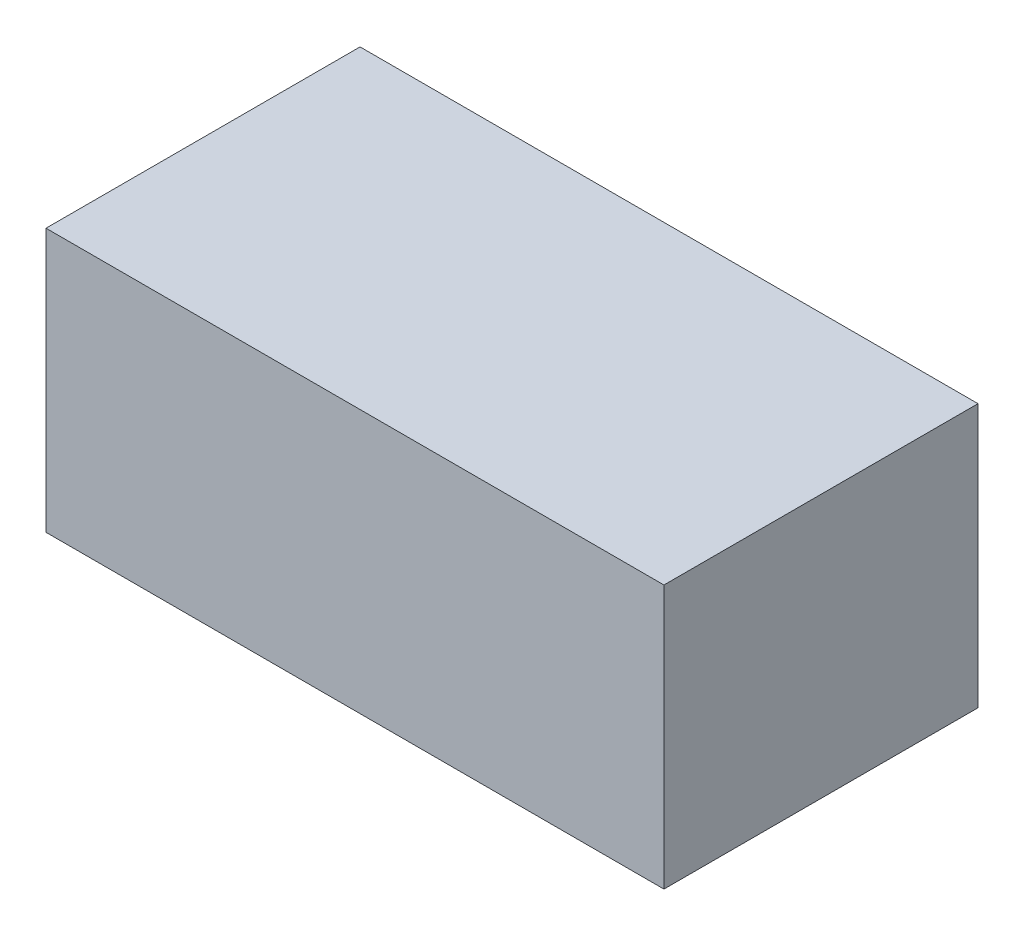
SolidWorks part; units mm, degrees
ref_plane "Front Plane" through (0, 0, 0) normal (0, 0, 1) x (1, 0, 0)
ref_plane "Top Plane" through (0, 0, 0) normal (0, 1, 0) x (1, 0, 0)
ref_plane "Right Plane" through (0, 0, 0) normal (1, 0, 0) x (0, 0, -1)
other "Center of Mass"
sketch "Sketch1" plane through (0, 0, 0) normal (0, 1, 0) x (1, 0, 0)
  line L1 (0, 0) -> (305, 0)
  line L2 (0, 0) -> (0, 155)
  line L3 (0, 155) -> (305, 155)
  line L4 (305, 0) -> (305, 155)
  dimension "D1" = 155
  dimension "D2" = 305
extrude "Boss-Extrude1" add sketch "Sketch1" along normal blind 130
